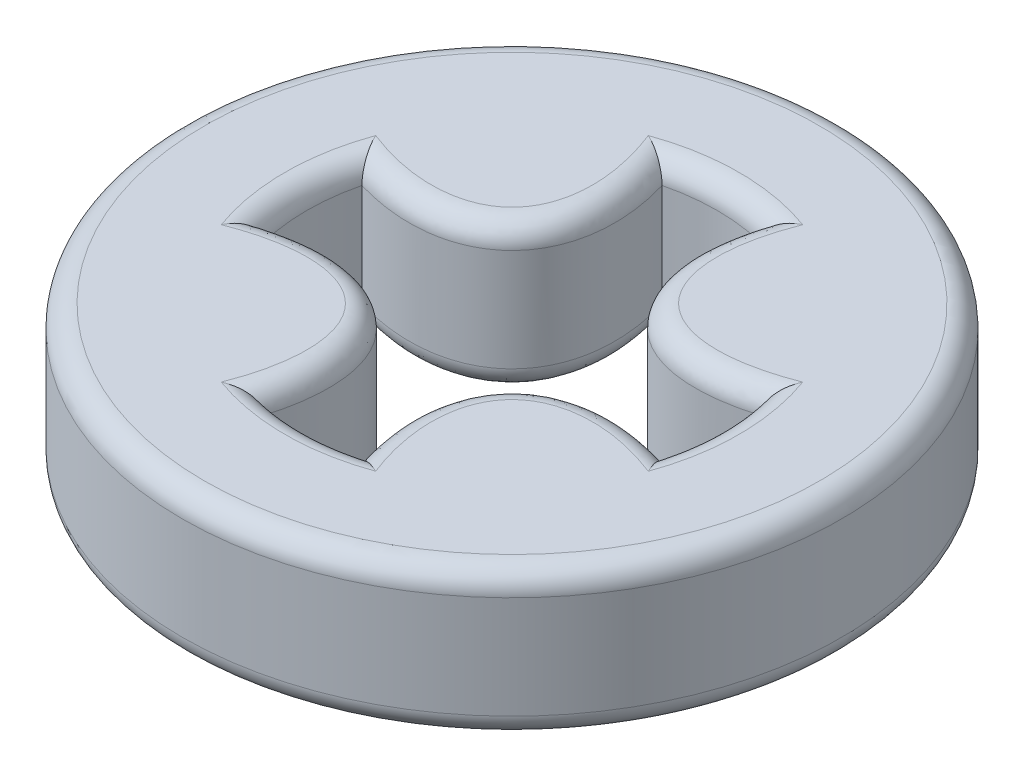
SolidWorks part; units mm, degrees
ref_plane "Front Plane" through (0, 0, 0) normal (0, 0, 1) x (1, 0, 0)
ref_plane "Top Plane" through (0, 0, 0) normal (0, 1, 0) x (1, 0, 0)
ref_plane "Right Plane" through (0, 0, 0) normal (1, 0, 0) x (0, 0, -1)
sketch "Sketch4" plane through (0, 0, 0) normal (0, 1, 0) x (1, 0, 0)
  circle A0 centre (0, 0) radius 4.5
extrude "Boss-Extrude3" add sketch "Sketch4" along normal blind 2
sketch "Sketch3" plane through (0, 0, 0) normal (0, 1, 0) x (1, 0, 0)
  arc A4 (-2.7188, 0.6695) -> (-2.7188, -0.6695) centre (0, 0) ccw
  arc A5 (0.6695, 2.7188) -> (-0.6695, 2.7188) centre (0, 0) ccw
  arc A6 (2.7188, -0.6695) -> (2.7188, 0.6695) centre (0, 0) ccw
  arc A7 (-0.6695, -2.7188) -> (0.6695, -2.7188) centre (0, 0) ccw
  ellipse E0 centre (-3.4, 3.4) end of major axis (-5.875, 5.875) minor radius 2 (-2.7188, 0.6695) -> (-0.6695, 2.7188) ccw
  ellipse E1 centre (3.4, 3.4) end of major axis (5.875, 5.875) minor radius 2 (0.6695, 2.7188) -> (2.7188, 0.6695) ccw
  ellipse E2 centre (3.4, -3.4) end of major axis (5.875, -5.875) minor radius 2 (2.7188, -0.6695) -> (0.6695, -2.7188) ccw
  ellipse E3 centre (-3.4, -3.4) end of major axis (-5.875, -5.875) minor radius 2 (-0.6695, -2.7188) -> (-2.7188, -0.6695) ccw
  dimension "D1" = 5.6
extrude "Cut-Extrude2" cut sketch "Sketch3" along normal blind 2
fillet "Fillet1" radius 0.3 18 edges at (0, 0, 4.5) (0, 2, 4.5) (0, 0, 2.8) (0.925, 0, 0.925) (2.8, 0, 0) (0.925, 0, -0.925) (0, 0, -2.8) (-0.925, 0, -0.925) (-0.925, 0, 0.925) (-2.8, 0, 0) (-2.8, 2, 0) (2.8, 2, 0) (0.925, 2, 0.925) (0, 2, 2.8) (-0.925, 2, 0.925) (-0.925, 2, -0.925) (0.925, 2, -0.925) (0, 2, -2.8)
